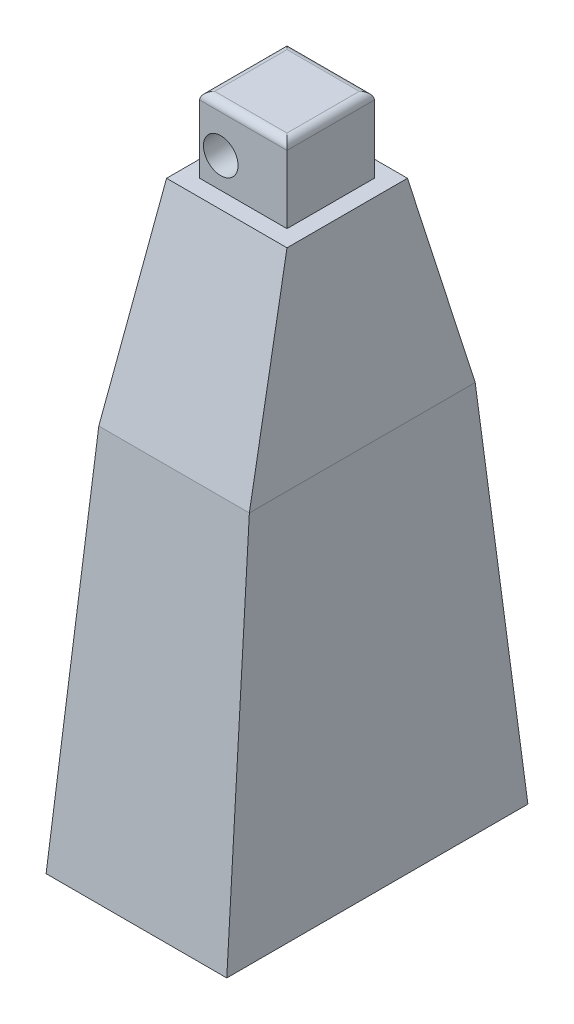
SolidWorks part; units mm, degrees
ref_plane "Front Plane" through (0, 0, 0) normal (0, 0, 1) x (1, 0, 0)
ref_plane "Top Plane" through (0, 0, 0) normal (0, 1, 0) x (1, 0, 0)
ref_plane "Right Plane" through (0, 0, 0) normal (1, 0, 0) x (0, 0, -1)
sketch "Sketch1" plane through (0, 0, 0) normal (0, 1, 0) x (1, 0, 0)
  line L1 (-12, 20) -> (12, 20)
  line L2 (-12, 20) -> (-12, -20)
  line L3 (-12, -20) -> (12, -20)
  line L4 (12, 20) -> (12, -20)
  line L5 (-12, 20) -> (12, -20) construction
  line L6 (-12, -20) -> (12, 20) construction
  point P0 (0, 0)
  dimension "D1" = 40
  dimension "D2" = 24
ref_plane "Plane1" through (0, 50, 0) normal (0, 1, 0) x (1, 0, 0)
sketch "Sketch2" plane through (0, 50, 0) normal (0, 1, 0) x (1, 0, 0)
  line L1 (10, 15) -> (-10, 15)
  line L2 (10, 15) -> (10, -15)
  line L3 (10, -15) -> (-10, -15)
  line L4 (-10, 15) -> (-10, -15)
  line L5 (10, 15) -> (-10, -15) construction
  line L6 (10, -15) -> (-10, 15) construction
  point P0 (0, 0)
  dimension "D1" = 30
  dimension "D2" = 20
loft "Loft1" add profiles "Sketch1", "Sketch2"
sketch "Sketch3" plane through (0, 50, 0) normal (0, 1, 0) x (1, 0, 0)
  line L4 (-10, 15) -> (-10, -15)
  line L5 (-10, -15) -> (10, -15)
  line L6 (10, -15) -> (10, 15)
  line L7 (10, 15) -> (-10, 15)
  line L8 (-10, 15) -> (-10, -15)
  line L9 (-10, -15) -> (10, -15)
  line L10 (10, -15) -> (10, 15)
  line L11 (10, 15) -> (-10, 15)
  dimension "D1" = 0
ref_plane "Plane2" through (0, 76, 0) normal (0, 1, 0) x (1, 0, 0)
sketch "Sketch4" plane through (0, 76, 0) normal (0, 1, 0) x (1, 0, 0)
  line L1 (8, 8) -> (-8, 8)
  line L2 (8, 8) -> (8, -8)
  line L3 (8, -8) -> (-8, -8)
  line L4 (-8, 8) -> (-8, -8)
  line L5 (8, 8) -> (-8, -8) construction
  line L6 (8, -8) -> (-8, 8) construction
  point P0 (0, 0)
  dimension "D1" = 16
loft "Loft2" add profiles "Sketch3", "Sketch4"
sketch "Sketch5" plane through (0, 76, 0) normal (0, 1, 0) x (1, 0, 0)
  line L26 (5.8, -5.8) -> (5.8, 5.8)
  line L27 (-5.8, -5.8) -> (5.8, -5.8)
  line L28 (-5.8, 5.8) -> (-5.8, -5.8)
  line L29 (5.8, 5.8) -> (-5.8, 5.8)
  line L30 (5.8, -5.8) -> (5.8, 5.8)
  line L31 (-5.8, -5.8) -> (5.8, -5.8)
  line L32 (-5.8, 5.8) -> (-5.8, -5.8)
  line L33 (5.8, 5.8) -> (-5.8, 5.8)
  dimension "D1" = 2.2
extrude "Boss-Extrude1" add sketch "Sketch5" along normal blind 10
sketch "Sketch6" plane through (0, 0, 5.8) normal (0, 0, 1) x (1, 0, 0)
  line L0 (-5.8, 76) -> (5.8, 76) construction
  line L3 (0, 86) -> (0, 76) construction
  line L4 (-5.8, 86) -> (5.8, 86) construction
  line L5 (-8, 76) -> (8, 76) construction
  circle A0 centre (-3, 80) radius 2.3
  dimension "D1" = 4.6
  dimension "D2" = 4
  dimension "D3" = 3
extrude "Cut-Extrude1" cut sketch "Sketch6" against normal blind 6
sketch "Sketch7" plane through (0, 0, -5.8) normal (0, 0, -1) x (-1, 0, 0)
  line L0 (0, 86) -> (0, 76) construction
  line L1 (-5.8, 86) -> (5.8, 86) construction
  line L2 (-8, 76) -> (8, 76) construction
  line L3 (-5.8, 76) -> (5.8, 76) construction
  circle A0 centre (-3, 80) radius 2.3
  dimension "D1" = 4.6
  dimension "D2" = 3
  dimension "D3" = 4
extrude "Cut-Extrude2" cut sketch "Sketch7" against normal blind 6
fillet "Fillet1" radius 1 4 edges at (0, 86, 5.8) (-5.8, 86, 0) (0, 86, -5.8) (5.8, 86, 0)
sketch "Sketch8" plane through (0, 0, 0) normal (0, -1, 0) x (1, 0, 0)
  line L14 (-4.2, -12.2) -> (4.2, -12.2)
  line L15 (4.2, -12.2) -> (4.2, 12.2)
  line L16 (-4.2, 12.2) -> (-4.2, -12.2)
  line L17 (4.2, 12.2) -> (-4.2, 12.2)
  line L18 (-4.2, -12.2) -> (4.2, -12.2)
  line L19 (4.2, -12.2) -> (4.2, 12.2)
  line L20 (-4.2, 12.2) -> (-4.2, -12.2)
  line L21 (4.2, 12.2) -> (-4.2, 12.2)
  dimension "D1" = 7.8
extrude "Cut-Extrude3" cut sketch "Sketch8" against normal blind 20
sketch "Sketch9" plane through (0, 0, 0) normal (0, -1, 0) x (1, 0, 0)
  line L0 (0, 20) -> (0, 0) construction
  line L1 (-12, 20) -> (12, 20) construction
  line L2 (0, 19) -> (1.7061, 19) construction
  line L3 (0, 0) -> (4.2, 0) construction
  line L4 (4.2, -12.2) -> (4.2, 12.2) construction
  circle A0 centre (0, 16) radius 2.3
  circle A1 centre (0, 16) radius 3 construction
  circle A2 centre (0, -16) radius 2.3
  dimension "D1" = 4.6
  dimension "D2" = 6
  dimension "D3" = 1
extrude "Cut-Extrude4" cut sketch "Sketch9" against normal blind 6
